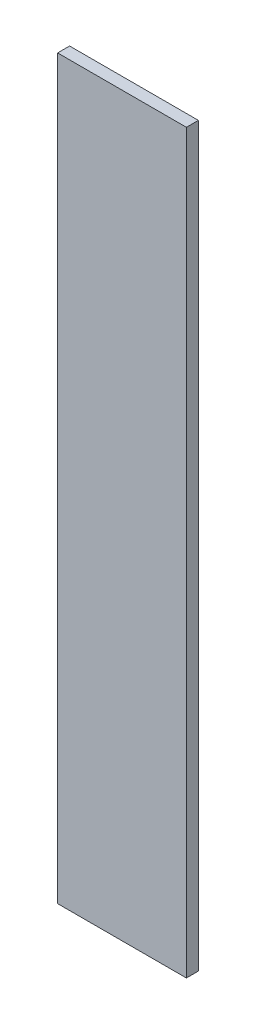
SolidWorks part; units mm, degrees
ref_plane "Plan de face" through (0, 0, 0) normal (0, 0, 1) x (1, 0, 0)
ref_plane "Plan de dessus" through (0, 0, 0) normal (0, 1, 0) x (1, 0, 0)
ref_plane "Plan de droite" through (0, 0, 0) normal (1, 0, 0) x (0, 0, -1)
sketch "Esquisse1" plane through (0, 0, 0) normal (0, 0, 1) x (1, 0, 0)
  line L1 (-30.9125, 20.8688) -> (22.8375, 20.8688)
  line L2 (-30.9125, 20.8688) -> (-30.9125, -286.6313)
  line L3 (-30.9125, -286.6313) -> (22.8375, -286.6313)
  line L4 (22.8375, 20.8688) -> (22.8375, -286.6313)
  dimension "D1" = 53.75
  dimension "D2" = 307.5
extrude "Boss.-Extru.4" add sketch "Esquisse1" along normal blind 5
